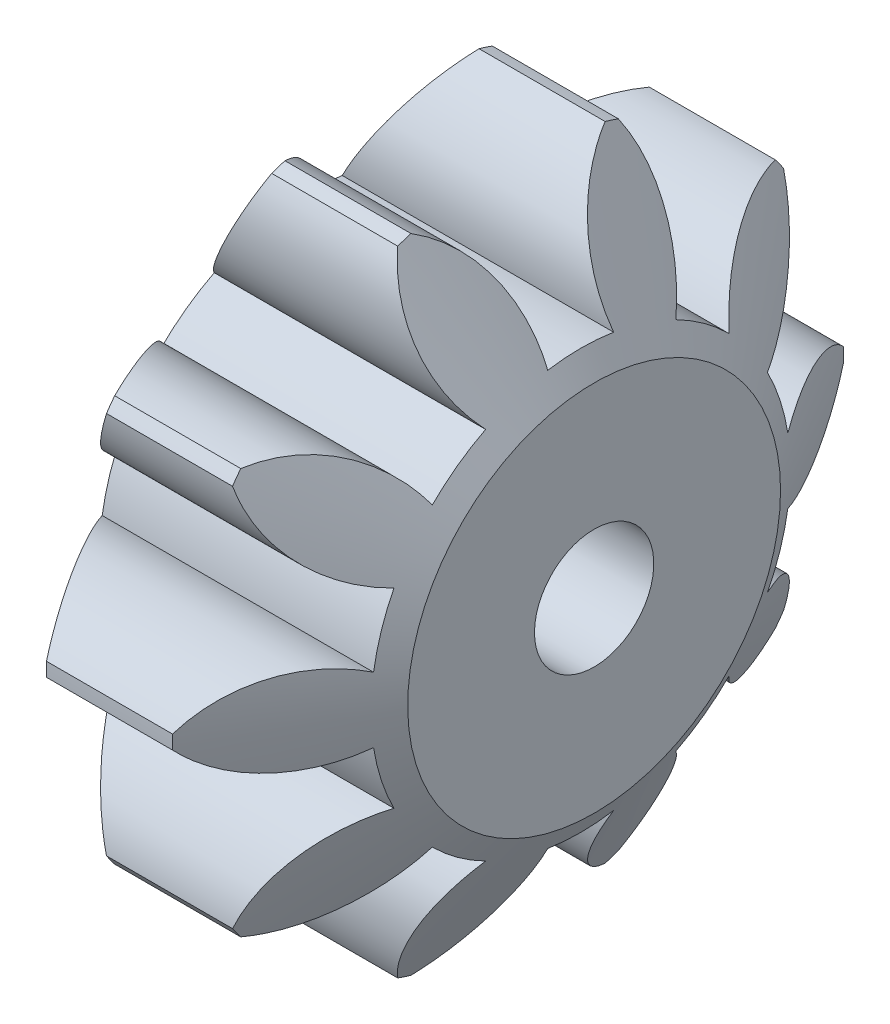
SolidWorks part; units mm, degrees
ref_plane "Plane1" through (0, 0, 0) normal (0, 0, 1) x (1, 0, 0)
ref_plane "Plane2" through (0, 0, 0) normal (0, 1, 0) x (1, 0, 0)
ref_plane "Plane3" through (0, 0, 0) normal (1, 0, 0) x (0, 0, -1)
sketch "HoldingSke" plane through (0, 0, 0) normal (0, 1, 0) x (1, 0, 0)
  line L0 (0, 0) -> (0.6565, -0.1158)
  line L1 (-15, 0) -> (100, 0) construction
  line L2 (0, 0) -> (-2.1039, 2.3779)
  line L3 (0, 0) -> (-11.863, 4.5341)
  line L4 (0, 0) -> (8.5048, 1.4996)
  line L5 (0, 0) -> (-46.8476, -17.4728)
  line L6 (0, 0) -> (-6.6317, -4.4744)
  line L7 (-2.1039, 2.3779) -> (8.6586, 51.2059)
  line L8 (-76.2, 54.61) -> (-75.7, 54.61)
  line L9 (-71.009, 38.7566) -> (-53.1078, 45.2721)
  line L10 (-76.2, 71.12) -> (104.1128, 71.12)
  line L11 (0, 0) -> (-8, 0)
  line L12 (-76.2, 101.6) -> (-76.147, 101.6)
  line L13 (24.9733, 27.94) -> (52.9518, 28.4284)
  line L14 (24.9733, 27.94) -> (24.9743, 27.94)
  line L15 (24.9733, 27.94) -> (100.4006, 29.5858)
  line L16 (-63.627, -1.5) -> (-12.827, -1.5)
  circle A0 centre (0, 0) radius 1.5
  circle A1 centre (0, 0) radius 5.624
  circle A2 centre (0, 0) radius 37.5
  circle A3 centre (0, 0) radius 1.5
  dimension "MHD" = 11.248
  dimension "Hub_dia" = 75
  dimension "Bore" = 3
  dimension "MBD" = 3
  dimension "Num_teeth" = 10
  dimension "Pitch" = 0.6667
  dimension "Overall_len" = 50
  dimension "Show_teeth" = 10
  dimension "Thickness" = 8
  dimension "OAL" = 50.0001
  dimension "T_dim" = 0.5
  dimension "Ap" = 20
  dimension "H" = 19.05
  dimension "Pitch_radius" = 180.3128
  dimension "Width" = 8
  dimension "Backlash" = 0.053
  dimension "Addendum_fac" = 1
  dimension "Dedendum_fac" = 1.25
  dimension "Clearance_fac" = 0.25
  dimension "Dedendum_add" = 0.001
  dimension "Module" = 1.5
sketch "BasProSke" plane through (0, 0, 0) normal (0, 1, 0) x (1, 0, 0)
  line L0 (-10, 0) -> (60, 0) construction
  line L1 (0, 0) -> (0, 9)
  line L2 (0, 0) -> (8, 0)
  line L3 (8, 0) -> (8, 9)
  line L4 (8, 9) -> (0, 9)
  dimension "Thickness" = 8
  dimension "Diameter" = 18
revolve "Base-Revolve" add sketch "BasProSke" angle 360 about L0
sketch "TooCutSke" plane through (0, 0, 0) normal (1, 0, 0) x (0, 0, -1)
  line L1 (0, 0) -> (0, 107) construction
  line L2 (0, 0) -> (-1.2658, 7.3924) construction
  line L3 (0, 0) -> (-4.5869, 14.117) construction
  line L4 (-1.2658, 7.3924) -> (-2.2934, 7.0585) construction
  arc A0 (0.8839, 5.5541) -> (-0.8839, 5.5541) centre (0, 0) ccw
  arc A1 (2.6378, 8.6313) -> (-2.6378, 8.6313) centre (0, 0) ccw
  circle A2 centre (0, 0) radius 7.5 construction
  circle A3 centre (0, 0) radius 7.0477 construction
  arc A4 (-0.8839, 5.5541) -> (-2.6378, 8.6313) centre (-3.8646, 5.8936) ccw
  arc A5 (2.6378, 8.6313) -> (0.8839, 5.5541) centre (3.8646, 5.8936) ccw
  dimension "Root_dia" = 11.248
  dimension "Overcut_dia" = 18.0508
  dimension "Pitch_dia" = 15
  dimension "Base_dia" = 14.0954
  dimension "Flank_rad" = 3
  dimension "Half_ang" = 18
  dimension "Half_CT" = 1.0805
extrude "ToothCut" cut sketch "TooCutSke" along normal through all
fillet "Breaks" [suppressed] radius 0.03
fillet "RootFillets" [suppressed] radius 0.376
pattern_circular "TeethCuts" count 10 every 36 about axis through (-10, 0, 0) along (1, 0, 0) of "ToothCut", "RootFillets", "Breaks"
sketch "HubNeaOneSke" plane through (0, 0, 0) normal (-1, 0, 0) x (0, 0, 1)
  circle A0 centre (0, 0) radius 5.624
  dimension "Diameter" = 11.248
extrude "HubNearOne" [suppressed] add sketch "HubNeaOneSke" along normal blind 42.0001
sketch "HubNeaBotSke" plane through (0, 0, 0) normal (-1, 0, 0) x (0, 0, 1)
  circle A0 centre (0, 0) radius 5.624
  dimension "Diameter" = 11.248
extrude "HubNearBoth" [suppressed] add sketch "HubNeaBotSke" along normal blind 21
ref_plane "FarPln" through (8, 0, 0) normal (1, 0, 0) x (0, 0, -1)
sketch "HubFarSke" plane through (8, 0, 0) normal (1, 0, 0) x (0, 0, -1)
  circle A0 centre (0, 0) radius 5.624
  dimension "Diameter" = 11.248
extrude "HubFar" [suppressed] add sketch "HubFarSke" along normal blind 21
sketch "BorSke" plane through (0, 0, 0) normal (1, 0, 0) x (0, 0, -1)
  circle A0 centre (0, 0) radius 1.5
  dimension "Diameter" = 3
extrude "Bore" cut sketch "BorSke" along normal mid plane 100.0001
sketch "KeySke" plane through (0, 0, 0) normal (1, 0, 0) x (0, 0, -1)
  line L0 (-0.6, 0) -> (-0.6, 2)
  line L1 (-0.6, 2) -> (0.6, 2)
  line L2 (0.6, 2) -> (0.6, 0)
  line L3 (0, 0) -> (0, 34) construction
  line L4 (-0.6, 0) -> (0.6, 0)
  dimension "Offset" = 2
  dimension "Width" = 1.2
extrude "Keyway" [suppressed] cut sketch "KeySke" along normal mid plane 100.0001
pattern_circular "Keyway2" [suppressed] count 2 every 90 about axis through (-10, 0, 0) along (1, 0, 0)
sketch "Sketch1" plane through (0, 0, 0) normal (0, 1, 0) x (1, 0, 0)
  line L0 (0, 0) -> (-6.6975, 0) construction
  line L1 (0, 0.8839) -> (0, -0.8839) construction
  line L2 (0, -5) -> (3.9466, -11.8356)
  line L3 (3.9466, -11.8356) -> (4.0534, -11.8356)
  line L4 (4.0534, -11.8356) -> (8, -5)
  line L5 (8, -5) -> (10.0928, -15.9084)
  line L6 (10.0928, -15.9084) -> (-2.2129, -14.525)
  line L7 (-2.2129, -14.525) -> (0, -5)
  line L8 (8, -2.6029) -> (8, -0.8646) construction
  line L9 (0, -0.8646) -> (0, -2.6029) construction
  line L10 (0, -5.5554) -> (0, -8.9981) construction
  line L11 (8, -8.9981) -> (8, -5.5554) construction
  dimension "D1" = 5
  dimension "D2" = 30
  dimension "D3" = 30
revolve "Cut-Revolve1" cut sketch "Sketch1" angle 360 about L0
sketch "Sketch2" plane through (0, 0, 0) normal (-1, 0, 0) x (0, 0, 1)
  circle A0 centre (0, 0) radius 1.6
  dimension "D1" = 3.2
extrude "Cut-Extrude1" cut sketch "Sketch2" against normal blind 10
equation "' \"Module@HoldingSke\" = 6.35"
equation "' \"Num_teeth@HoldingSke\" = 12"
equation "' \"Ap@HoldingSke\" =  20"
equation "' \"Ap@HoldingSke\" = 20"
equation "' \"Width@HoldingSke\" = 0.5 * 25.4"
equation "' \"Hub_dia@HoldingSke\"= 1 * 25.4"
equation "' \"Hub_dia@HoldingSke\" = 1 * 25.4"
equation "' \"Overall_len@HoldingSke\" = 1.0 * 25.4"
equation "' \"Bore@HoldingSke\" = 0.75 * 25.4"
equation "' \"T_dim@HoldingSke\" = 0.1 * 25.4"
equation "' \"Width@KeySke\" = 0.25 * 25.4"
equation "' \"Show_teeth@HoldingSke\" = 13"
equation "' \"Backlash@HoldingSke\" = 0.009 * 25.4"
equation "' \"Addendum_fac@HoldingSke\" = 1.0"
equation "' \"Dedendum_fac@HoldingSke\" = 1.25"
equation "' \"Dedendum_add@HoldingSke\" = 0.00005 * 25.4"
equation "' \"Clearance_fac@HoldingSke\" = 0.25"
equation "\"Pitch@HoldingSke\" = 1 / \"Module@HoldingSke\""
equation "\"Overcut_dia@TooCutSke\" = (\"Num_teeth@HoldingSke\" + 2 * \"Addendum_fac@HoldingSke\") / \"Pitch@HoldingSke\" + 0.002 * 25.4"
equation "\"Pitch_dia@TooCutSke\" = \"Num_teeth@HoldingSke\" / \"Pitch@HoldingSke\""
equation "\"Base_dia@TooCutSke\" = \"Num_teeth@HoldingSke\" / \"Pitch@HoldingSke\" * cos((\"Ap@HoldingSke\"  * 3.14159265 / 180))"
equation "\"Root_dia@TooCutSke\" = (\"Num_teeth@HoldingSke\" + 2) / \"Pitch@HoldingSke\" - 2 * (\"Addendum_fac@HoldingSke\" + \"Dedendum_fac@HoldingSke\") / \"Pitch@HoldingSke\" - \"Dedendum_add@HoldingSke\" * 2"
equation "\"Half_ang@TooCutSke\" = 180 / \"Num_teeth@HoldingSke\""
equation "\"Half_CT@TooCutSke\" = \"Num_teeth@HoldingSke\" / \"Pitch@HoldingSke\" * sin((3.14159265 / 2 / \"Num_teeth@HoldingSke\")) / 2 - 7 * \"Backlash@HoldingSke\" / 4"
equation "\"Flank_rad@TooCutSke\" = \"Num_teeth@HoldingSke\" / \"Pitch@HoldingSke\" / 5"
equation "\"Radius@RootFillets\" = \"Clearance_fac@HoldingSke\" / \"Pitch@HoldingSke\" + \"Dedendum_add@HoldingSke\""
equation "\"Break_rad@Breaks\" = 0.02 / \"Pitch@HoldingSke\""
equation "\"Thickness@HoldingSke\" = \"Width@HoldingSke\""
equation "\"OAL@HoldingSke\" = \"Thickness@HoldingSke\""
equation "\"MHD@HoldingSke\" = (\"Num_teeth@HoldingSke\" + 2) / \"Pitch@HoldingSke\" - 2 * (\"Addendum_fac@HoldingSke\" + \"Dedendum_fac@HoldingSke\")  / \"Pitch@HoldingSke\" - \"Dedendum_add@HoldingSke\" * 2"
equation "\"MBD@HoldingSke\" = (\"Num_teeth@HoldingSke\" + 2) / \"Pitch@HoldingSke\" - 2 * (\"Addendum_fac@HoldingSke\" + \"Dedendum_fac@HoldingSke\")  / \"Pitch@HoldingSke\" - \"Dedendum_add@HoldingSke\" * 2 - 0.002 * 25.4"
equation "\"MHD@HoldingSke\" = ((sgn( \"MHD@HoldingSke\" - \"Hub_dia@HoldingSke\" )-1)*( \"MHD@HoldingSke\" - \"Hub_dia@HoldingSke\" ))/-2+ \"Hub_dia@HoldingSke\""
equation "\"MBD@HoldingSke\" = ((sgn( \"MBD@HoldingSke\" - \"Bore@HoldingSke\" )-1)*( \"MBD@HoldingSke\" - \"Bore@HoldingSke\" ))/-2+ \"Bore@HoldingSke\""
equation "\"OAL@HoldingSke\" = ((sgn( \"OAL@HoldingSke\" - \"Overall_len@HoldingSke\" )+1)*( \"OAL@HoldingSke\" - \"Overall_len@HoldingSke\" ))/2 + \"Overall_len@HoldingSke\" + 0.000002 * 25.4"
equation "\"Num_teeth@TeethCuts\" = int( \"Show_teeth@HoldingSke\" ) + 1"
equation "\"Num_teeth@TeethCuts\" = ((sgn( \"Num_teeth@TeethCuts\" - \"Num_teeth@HoldingSke\" )-1)*( \"Num_teeth@TeethCuts\" - \"Num_teeth@HoldingSke\" ))/-2+ \"Num_teeth@HoldingSke\""
equation "\"Num_teeth@TeethCuts\" = ((sgn( \"Num_teeth@TeethCuts\" - 2.0)+1)*( \"Num_teeth@TeethCuts\" - 2.0))/2 +2.0"
equation "\"Angle@TeethCuts\" = 360.0 / \"Num_teeth@HoldingSke\""
equation "\"Diameter@BasProSke\" = (\"Num_teeth@HoldingSke\" + 2 * \"Addendum_fac@HoldingSke\") / \"Pitch@HoldingSke\""
equation "\"Thickness@BasProSke\"  = \"Thickness@HoldingSke\""
equation "' \"Fillet_rad@BasProSke\" =  \"Thickness@HoldingSke\" * 0.05"
equation "' \"Fillet_rad@BasProSke\" = \"Thickness@HoldingSke\" * 0.05"
equation "\"MHD@HoldingSke\" = ((sgn( \"MHD@HoldingSke\" - \"Root_dia@TooCutSke\" )-1)*( \"MHD@HoldingSke\" - \"Root_dia@TooCutSke\" ))/-2+ \"Root_dia@TooCutSke\""
equation "\"Diameter@HubNeaOneSke\" = \"MHD@HoldingSke\""
equation "\"Length@HubNearOne\" = \"OAL@HoldingSke\" - \"Thickness@BasProSke\""
equation "\"Diameter@HubNeaBotSke\" = \"MHD@HoldingSke\""
equation "\"Length@HubNearBoth\" = ( \"OAL@HoldingSke\" - \"Thickness@BasProSke\" ) / 2.0"
equation "\"Thickness@FarPln\" = \"Thickness@BasProSke\""
equation "\"Diameter@HubFarSke\" = \"MHD@HoldingSke\""
equation "\"Length@HubFar\" = ( \"OAL@HoldingSke\" - \"Thickness@BasProSke\" ) / 2.0"
equation "\"Diameter@BorSke\" = \"MBD@HoldingSke\""
equation "\"D1@Bore\" = \"OAL@HoldingSke\" * 2.0"
equation "\"D1@Keyway\" = \"OAL@HoldingSke\" * 2.0"
equation "\"Offset@KeySke\" = \"T_dim@HoldingSke\" + \"MBD@HoldingSke\" / 2.0"
